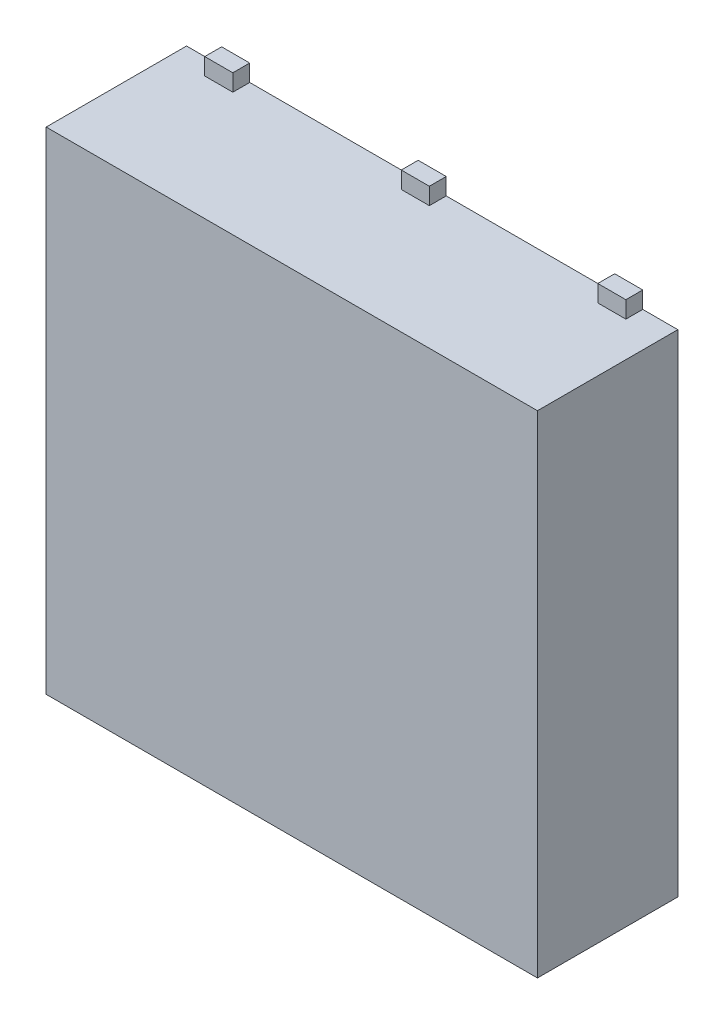
SolidWorks part; units mm, degrees
ref_plane "Plan de face" through (0, 0, 0) normal (0, 0, 1) x (1, 0, 0)
ref_plane "Plan de dessus" through (0, 0, 0) normal (0, 1, 0) x (1, 0, 0)
ref_plane "Plan de droite" through (0, 0, 0) normal (1, 0, 0) x (0, 0, -1)
sketch "Esquisse1" plane through (0, 0, 0) normal (0, 0, 1) x (1, 0, 0)
  line L0 (0, 2.1176) -> (0, -2.1176) construction
  line L1 (-3.5211, 0) -> (3.6146, 0) construction
  line L3 (-1.75, 1.75) -> (1.75, 1.75)
  line L4 (-1.75, 1.75) -> (-1.75, -1.75)
  line L5 (-1.75, -1.75) -> (1.75, -1.75)
  line L6 (1.75, 1.75) -> (1.75, -1.75)
  dimension "D1" = 3.5
  dimension "D2" = 3.5
extrude "Boss.-Extru.1" add sketch "Esquisse1" along normal blind 1
sketch "Esquisse2" plane through (0, 1.75, 0) normal (0, 1, 0) x (1, 0, 0)
  line L0 (1.75, 0) -> (-1.75, 0) construction
  line L1 (-0.1, 0) -> (0.1, 0)
  line L2 (-0.1, 0) -> (-0.1, -0.1202)
  line L3 (-0.1, -0.1202) -> (0.1, -0.1202)
  line L4 (0.1, 0) -> (0.1, -0.1202)
  line L5 (-2.1221, 0) -> (2.1631, 0) construction
  line L6 (0, 0.5007) -> (0, -1.1872) construction
  dimension "D1" = 0.2
  dimension "D2" = 0.1202
extrude "Boss.-Extru.2" add sketch "Esquisse2" along normal blind 0.12
pattern_linear "Répétition linéaire1" count 2 spacing 1.4 along (-1, 0, 0) of "Boss.-Extru.2"
pattern_linear "Répétition linéaire2" count 2 spacing 1.4 along (1, 0, 0) of "Boss.-Extru.2"
mirror "Symétrie1" about plane through (0, 0, 0) normal (0, 1, 0) of "Répétition linéaire2", "Boss.-Extru.2", "Répétition linéaire1"
